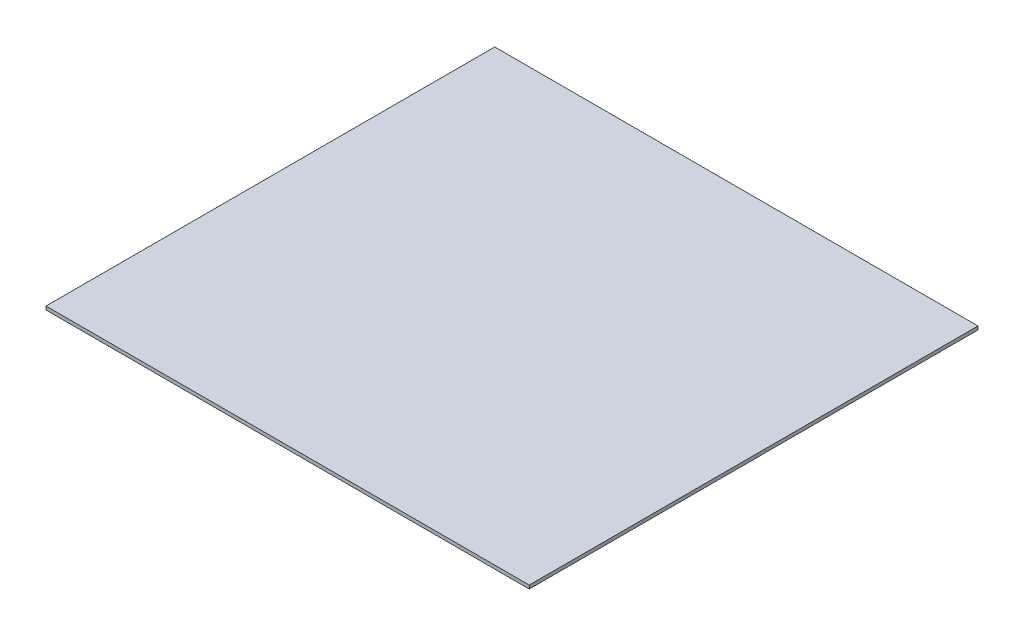
SolidWorks part; units mm, degrees
ref_plane "Front Plane" through (0, 0, 0) normal (0, 0, 1) x (1, 0, 0)
ref_plane "Top Plane" through (0, 0, 0) normal (0, 1, 0) x (1, 0, 0)
ref_plane "Right Plane" through (0, 0, 0) normal (1, 0, 0) x (0, 0, -1)
sketch "Sketch2" plane through (0, 0, 0) normal (0, 1, 0) x (1, 0, 0)
  line L1 (-36.3953, 25.1163) -> (33.6047, 25.1163)
  line L2 (-36.3953, 25.1163) -> (-36.3953, -39.8837)
  line L3 (-36.3953, -39.8837) -> (33.6047, -39.8837)
  line L4 (33.6047, 25.1163) -> (33.6047, -39.8837)
  dimension "D1" = 70
  dimension "D2" = 65
extrude "Boss-Extrude1" add sketch "Sketch2" along normal blind 0.5
